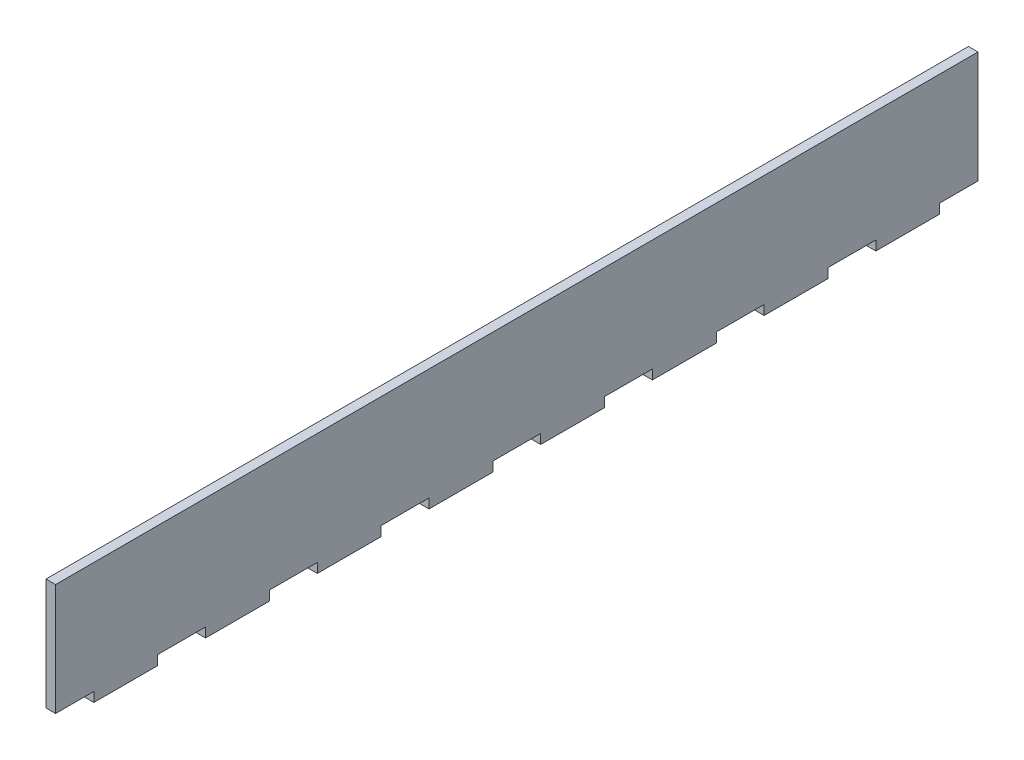
SolidWorks part; units mm, degrees
ref_plane "Front Plane" through (0, 0, 0) normal (0, 0, 1) x (1, 0, 0)
ref_plane "Top Plane" through (0, 0, 0) normal (0, 1, 0) x (1, 0, 0)
ref_plane "Right Plane" through (0, 0, 0) normal (1, 0, 0) x (0, 0, -1)
sketch "Sketch1" plane through (0, 0, 0) normal (1, 0, 0) x (0, 0, -1)
  line L0 (32, 0) -> (47, 0)
  line L1 (0, 0) -> (12, 0)
  line L2 (0, 0) -> (0, 35)
  line L3 (0, 35) -> (289, 35)
  line L4 (289, 0) -> (289, 35)
  line L7 (47, 0) -> (47, -3)
  line L8 (12, 0) -> (12, -3)
  line L9 (12, -3) -> (32, -3)
  line L10 (32, 0) -> (32, -3)
  line L13 (47, -3) -> (67, -3)
  line L14 (67, 0) -> (67, -3)
  line L15 (82, 0) -> (82, -3)
  line L16 (82, -3) -> (102, -3)
  line L17 (102, 0) -> (102, -3)
  line L18 (117, 0) -> (117, -3)
  line L19 (117, -3) -> (137, -3)
  line L20 (137, 0) -> (137, -3)
  line L21 (152, 0) -> (152, -3)
  line L22 (152, -3) -> (172, -3)
  line L23 (172, 0) -> (172, -3)
  line L24 (187, 0) -> (187, -3)
  line L25 (187, -3) -> (207, -3)
  line L26 (207, 0) -> (207, -3)
  line L27 (222, 0) -> (222, -3)
  line L28 (222, -3) -> (242, -3)
  line L29 (242, 0) -> (242, -3)
  line L30 (257, 0) -> (257, -3)
  line L31 (257, -3) -> (277, -3)
  line L32 (277, 0) -> (277, -3)
  line L33 (67, 0) -> (82, 0)
  line L34 (102, 0) -> (117, 0)
  line L35 (137, 0) -> (152, 0)
  line L36 (172, 0) -> (187, 0)
  line L37 (207, 0) -> (222, 0)
  line L38 (242, 0) -> (257, 0)
  line L39 (277, 0) -> (289, 0)
  point P10 (0, 0)
  point P12 (0, 0)
  dimension "D1" = 20
  dimension "D2" = 12
  dimension "D3" = 289
  dimension "D4" = 3
  dimension "D6" = 35
  dimension "D7" = 15
  dimension "D5" = 8
extrude "Boss-Extrude1" add sketch "Sketch1" along normal blind 3 contours L3 L4 L39 L32 L31 L30 L38 L29 L28 L27 L37 L26 L25 L24 L36 L23 L22 L21 L35 L20 L19 L18 L34 L17 L16 L15 L33 L14 L13 L7 L0 L10 L9 L8 L1 L2
